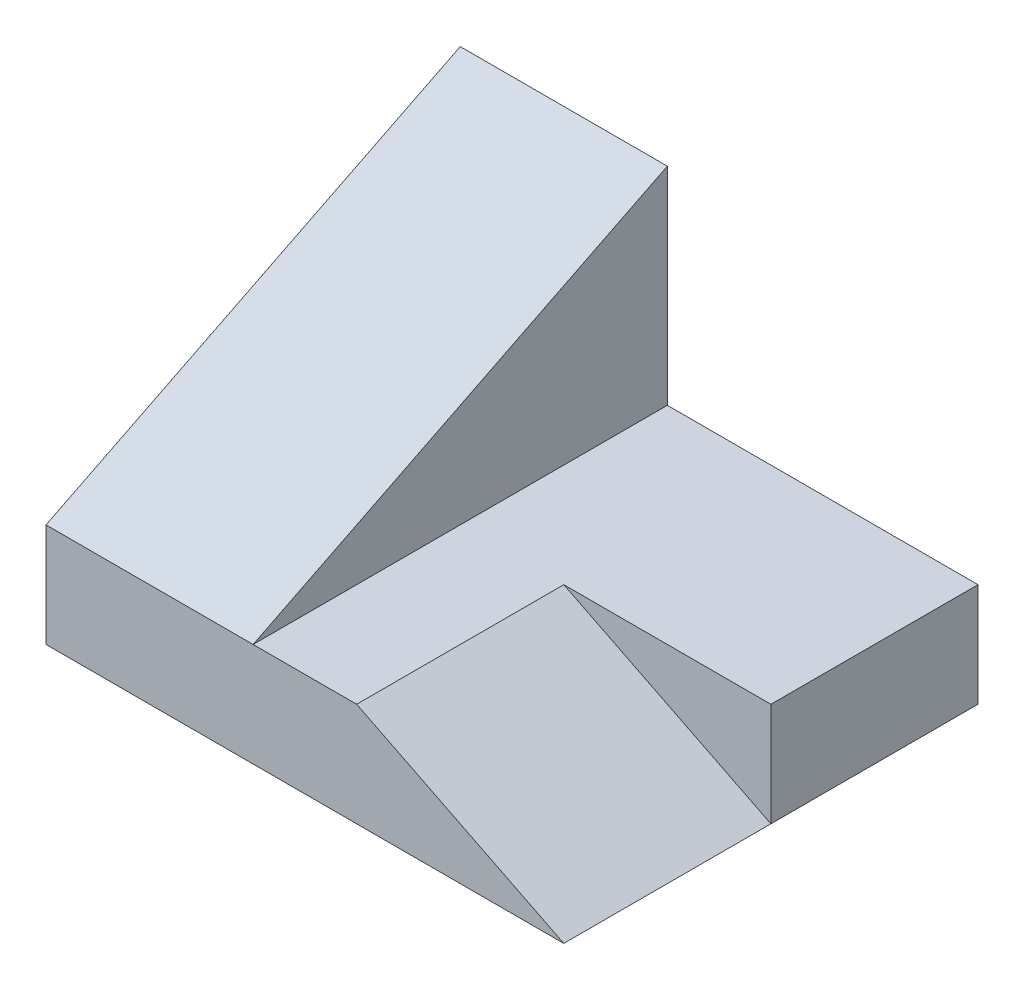
SolidWorks part; units mm, degrees
ref_plane "Front Plane" through (0, 0, 0) normal (0, 0, 1) x (1, 0, 0)
ref_plane "Top Plane" through (0, 0, 0) normal (0, 1, 0) x (1, 0, 0)
ref_plane "Right Plane" through (0, 0, 0) normal (1, 0, 0) x (0, 0, -1)
sketch "Sketch5" plane through (0, 0, 0) normal (0, 1, 0) x (1, 0, 0)
  line L1 (0, 0) -> (50, 0)
  line L2 (0, 0) -> (0, 40)
  line L3 (0, 40) -> (50, 40)
  line L4 (50, 0) -> (50, 40)
  dimension "D1" = 50
  dimension "D2" = 40
extrude "Boss-Extrude5" add sketch "Sketch5" along normal blind 10
sketch "Sketch6" plane through (0, 10, 0) normal (0, 1, 0) x (1, 0, 0)
  line L0 (0, 0) -> (50, 0) construction
  line L1 (0, 40) -> (20, 40)
  line L2 (0, 40) -> (0, 0)
  line L3 (0, 0) -> (20, 0)
  line L4 (20, 40) -> (20, 0)
  dimension "D1" = 20
extrude "Boss-Extrude6" add sketch "Sketch6" along normal blind 20
sketch "Sketch7" plane through (20, 0, 0) normal (1, 0, 0) x (0, 0, -1)
  line L0 (40, 30) -> (0, 10)
extrude "Cut-Extrude1" cut sketch "Sketch7" against normal blind 20 and the other way through all flip side to cut
sketch "Sketch8" plane through (0, 0, 0) normal (0, 0, 1) x (1, 0, 0)
  line L0 (50, 10) -> (30, 10)
  line L1 (20, 10) -> (50, 10) construction
  line L2 (30, 10) -> (50, 0)
  dimension "D1" = 20
extrude "Cut-Extrude2" cut sketch "Sketch8" against normal blind 20 and the other way through all
